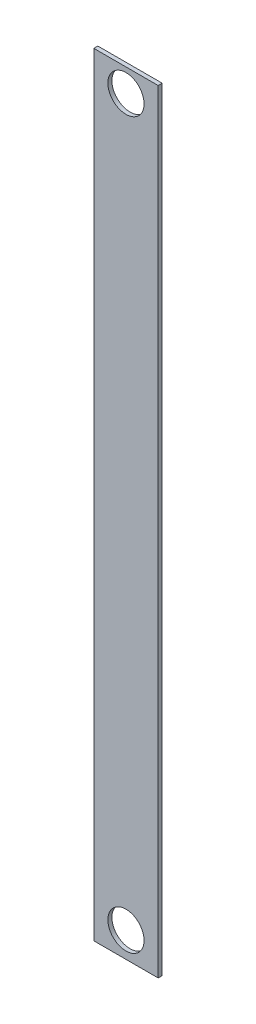
SolidWorks part; units mm, degrees
ref_plane "Front Plane" through (0, 0, 0) normal (0, 0, 1) x (1, 0, 0)
ref_plane "Top Plane" through (0, 0, 0) normal (0, 1, 0) x (1, 0, 0)
ref_plane "Right Plane" through (0, 0, 0) normal (1, 0, 0) x (0, 0, -1)
sketch "Sketch1" plane through (0, 0, 0) normal (0, 0, 1) x (1, 0, 0)
  line L1 (0, 0) -> (50.8, 0)
  line L2 (0, 0) -> (0, -609.6)
  line L3 (0, -609.6) -> (50.8, -609.6)
  line L4 (50.8, 0) -> (50.8, -609.6)
  dimension "D1" = 609.6
  dimension "D2" = 50.8
extrude "Boss-Extrude1" add sketch "Sketch1" along normal blind 3.175
sketch "Sketch2" plane through (0, 0, 3.175) normal (0, 0, 1) x (1, 0, 0)
  line L2 (0, -609.6) -> (50.8, -609.6) construction
  line L3 (0, -609.6) -> (50.8, -609.6) construction
  circle A0 centre (25.4, -18.1414) radius 14.279
  circle A1 centre (25.4, -589.6) radius 14.279
  point P9 (25.4, -609.6)
  dimension "D1" = 28.558
  dimension "D2" = 28.558
  dimension "D3" = 20
extrude "Cut-Extrude1" cut sketch "Sketch2" against normal through all
